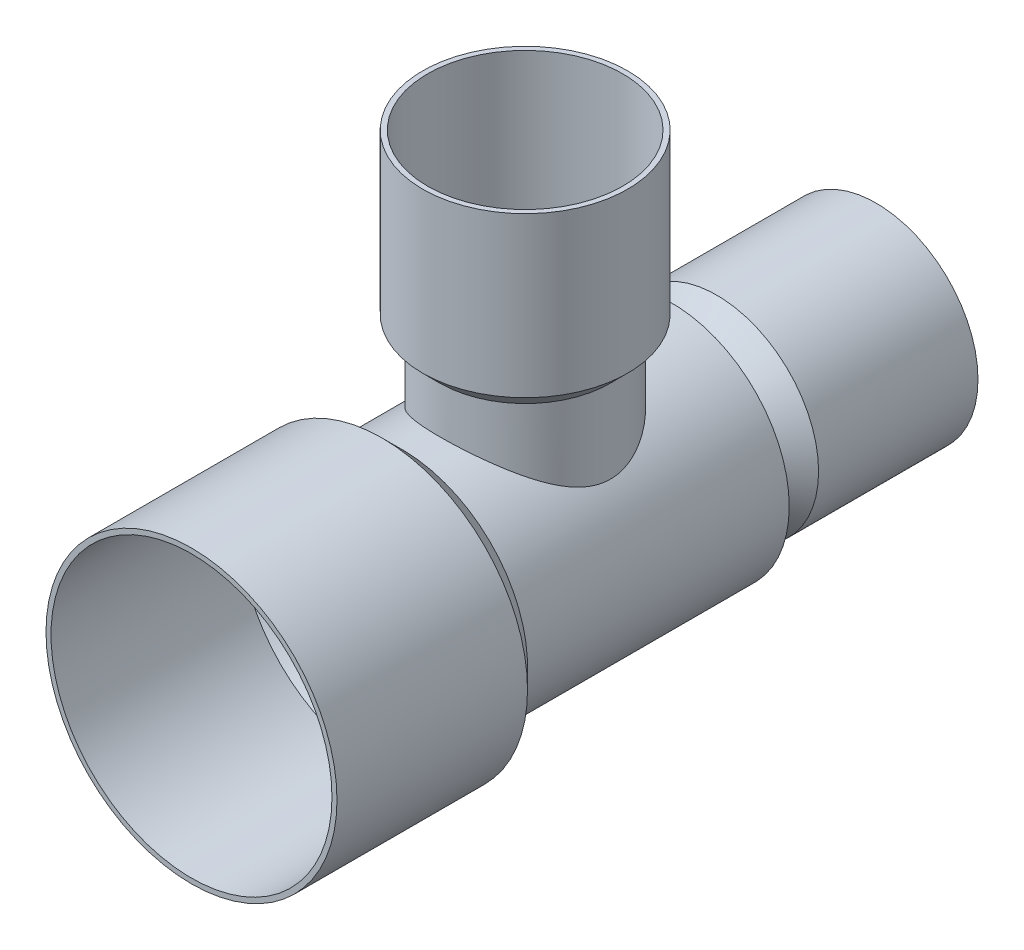
SolidWorks part; units mm, degrees
material "Copper"
ref_plane "Front" through (0, 0, 0) normal (0, 0, 1) x (1, 0, 0)
ref_plane "Top" through (0, 0, 0) normal (0, 1, 0) x (1, 0, 0)
ref_plane "Right" through (0, 0, 0) normal (1, 0, 0) x (0, 0, -1)
sketch "Sketch1" plane through (0, 0, 0) normal (1, 0, 0) x (0, 0, -1)
  line L0 (51.562, 0) -> (-49.022, 0)
  dimension "Length" = 100.584
  dimension "Mid" = 49.022
ref_plane "Plane3" through (0, 0, 49.022) normal (0, 0, 1) x (1, 0, 0)
sketch "Sketch2" plane through (0, 0, 49.022) normal (0, 0, 1) x (1, 0, 0)
  line L0 (0, 0) -> (16.51, 0) construction
  line L1 (16.51, 0) -> (17.2466, 0) construction
  circle A0 centre (0, 0) radius 17.2466 construction
  circle A1 centre (0, 0) radius 16.51
  dimension "Wall Thickness" = 0.7366
sweep "Sweep1" add profiles "Sketch2" path "Sketch1"
sketch "Sketch3" plane through (0, 0, 49.022) normal (0, 0, 1) x (1, 0, 0)
  line L0 (0, 0) -> (20.6375, 0) construction
  line L1 (20.6375, 0) -> (21.3741, 0) construction
  circle A0 centre (0, 0) radius 21.3741 construction
  circle A1 centre (0, 0) radius 20.6375
  dimension "A ID" = 41.275
  dimension "D1" = 0.7366
extrude "Extrude1" add sketch "Sketch3" against normal blind 27.686
sketch "Sketch4" plane through (0, 0, 21.336) normal (0, 0, -1) x (-1, 0, 0)
  circle A1 centre (0, 0) radius 20.6375 construction
  circle A2 centre (0, 0) radius 20.6375
extrude "Extrude2" add sketch "Sketch4" along normal blind 2.54 draft 45
sketch "Sketch9" plane through (0, 0, -51.562) normal (0, 0, -1) x (-1, 0, 0)
  circle A0 centre (0, 0) radius 14.224
  circle A1 centre (0, 0) radius 16.51
  circle A2 centre (0, 0) radius 16.51
  dimension "D2" = 28.448
  dimension "D1" = 0
extrude "Cut-Extrude4" cut sketch "Sketch9" against normal blind 23.114
sketch "Sketch10" plane through (0, 0, -28.448) normal (0, 0, -1) x (-1, 0, 0)
  circle A0 centre (0, 0) radius 14.224 construction
  circle A1 centre (0, 0) radius 16.51
  circle A2 centre (0, 0) radius 16.51
  circle A3 centre (0, 0) radius 14.224
  dimension "D1" = 0
extrude "Cut-Extrude5" cut sketch "Sketch10" against normal blind 3.81 draft 45 draft outward yes
sketch "Sketch11" plane through (0, 0, -24.638) normal (0, 0, -1) x (-1, 0, 0)
  circle A0 centre (0, 0) radius 10.414 construction
  circle A1 centre (0, 0) radius 10.414
extrude "Cut-Extrude6" cut sketch "Sketch11" against normal blind 3.81 draft 60 flip side to cut
ref_plane "Plane4" through (0, 37.338, 0) normal (0, 1, 0) x (-1, 0, 0)
sketch "Sketch5" plane through (0, 0, 0) normal (1, 0, 0) x (0, 0, -1)
  line L0 (11.7856, 24.384) -> (14.3256, 26.924)
  line L2 (14.3256, 26.924) -> (14.3256, 50.038)
  line L3 (11.7856, 24.384) -> (11.7856, 0)
  line L4 (51.562, 0) -> (-49.022, 0) construction
  line L5 (11.7856, 0) -> (0, 0)
  line L6 (0, 0) -> (0, 50.038)
  line L7 (14.3256, 50.038) -> (0, 50.038)
  line L8 (0, 50.038) -> (0, 31.2768) construction
  dimension "D1" = 50.038
  dimension "D2" = 14.3256
  dimension "D3" = 135
  dimension "D4" = 2.54
  dimension "D5" = 23.114
revolve "Revolve1" add sketch "Sketch5" angle 360 about L8
combine bodies "Combine1" operation type add bodies to combine 111 119
shell "Shell3" thickness 0.7366
equation "\"D1@Sketch3\"=\"Wall Thickness@Sketch2\""
equation "\"D1@Shell3\"=\"Wall Thickness@Sketch2\""
equation "\"D1@Fillet1\" = \"D2@Sketch8\"/3"
